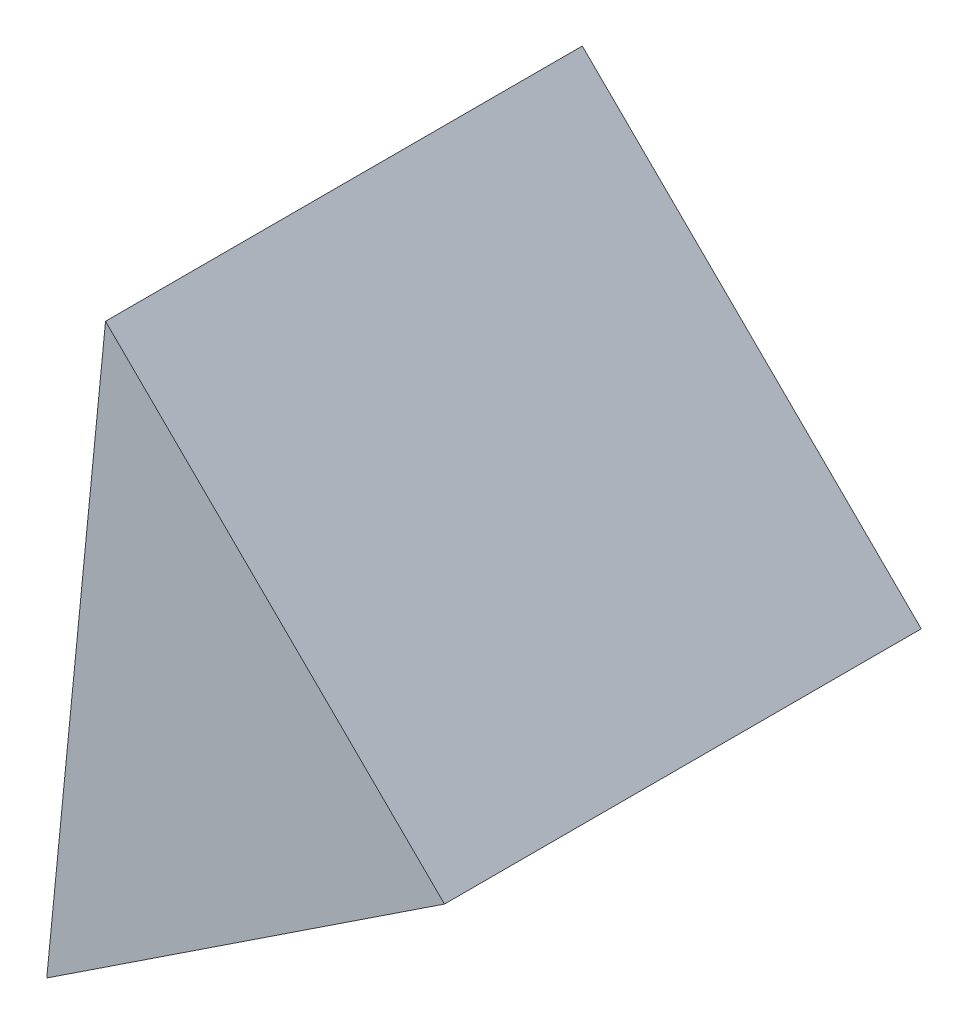
SolidWorks part; units mm, degrees
ref_plane "前视基准面" through (0, 0, 0) normal (0, 0, 1) x (1, 0, 0)
ref_plane "上视基准面" through (0, 0, 0) normal (0, 1, 0) x (1, 0, 0)
ref_plane "右视基准面" through (0, 0, 0) normal (1, 0, 0) x (0, 0, -1)
sketch "草图2" plane through (0, 0, 0) normal (0, 0, 1) x (1, 0, 0)
  line L0 (17.371, 11.8755) -> (3.1515, 25.9399)
  line L1 (17.371, 11.8755) -> (0.6862, 0.8475)
  line L2 (0.6862, 0.8475) -> (3.1515, 25.9399)
  dimension "D1" = 20
  dimension "D2" = 20
extrude "凸台-拉伸1" add sketch "草图2" along normal blind 20
